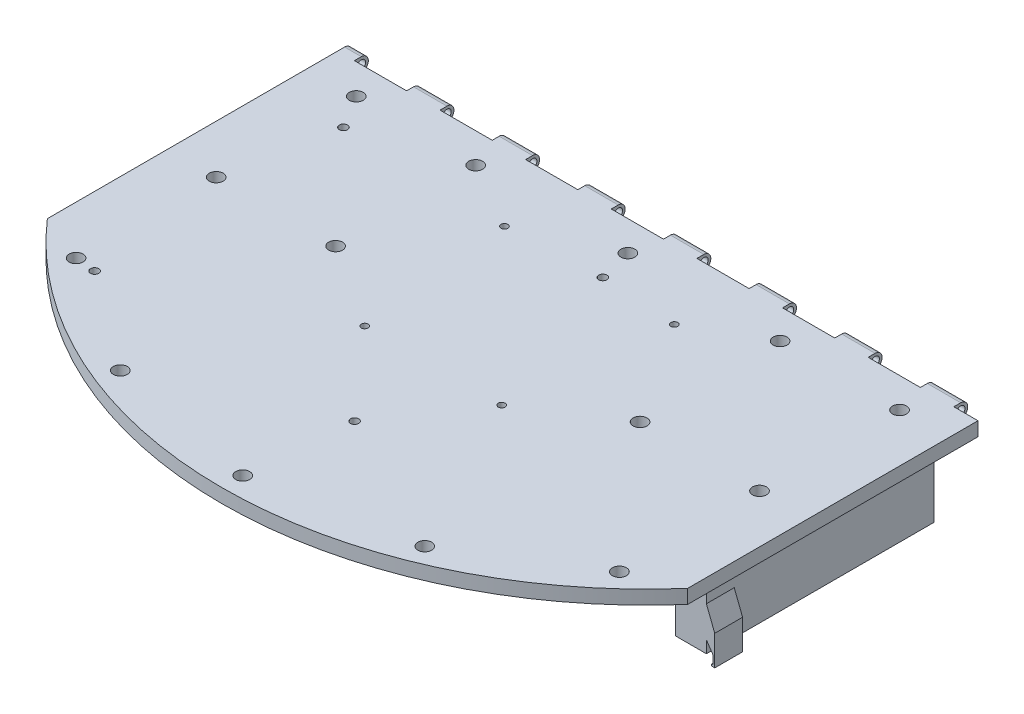
SolidWorks part; units mm, degrees
ref_plane "Front Plane" through (0, 0, 0) normal (0, 0, 1) x (1, 0, 0)
ref_plane "Top Plane" through (0, 0, 0) normal (0, 1, 0) x (1, 0, 0)
ref_plane "Right Plane" through (0, 0, 0) normal (1, 0, 0) x (0, 0, -1)
sketch "Sketch1" plane through (0, 0, 0) normal (0, 1, 0) x (1, 0, 0)
  line L0 (154.8848, 4.1371) -> (-154.8848, 4.1371)
  circle A0 centre (0, 0) radius 154.94
  arc A1 (154.8848, 4.1371) -> (-154.8848, 4.1371) centre (0, 0) cw
  dimension "D1" = 309.88
extrude "Boss-Extrude1" add sketch "Sketch1" along normal blind 5.08 contours L0 A0
sketch "Sketch2" plane through (0, 0, 0) normal (0, -1, 0) x (-1, 0, 0)
  line L0 (0, -154.94) -> (0, 4.1371) construction
  line L1 (-154.8848, 4.1371) -> (154.8848, 4.1371) construction
  line L8 (-112.1983, -7.3509) -> (-100.8687, -7.3509)
  line L9 (112.1983, -90.3509) -> (100.8687, -90.3509)
  line L10 (112.1983, -90.3509) -> (112.1983, -7.3509)
  line L11 (112.1983, -7.3509) -> (100.8687, -7.3509)
  line L12 (100.8687, -90.3509) -> (100.8687, -7.3509)
  line L13 (-112.1983, -90.3509) -> (-112.1983, -7.3509)
  line L14 (-112.1983, -90.3509) -> (-100.8687, -90.3509)
  line L15 (-100.8687, -90.3509) -> (-100.8687, -7.3509)
  arc A0 (-154.8848, 4.1371) -> (154.8848, 4.1371) centre (0, 0) ccw construction
extrude "Boss-Extrude2" add sketch "Sketch2" along normal blind 23.622
sketch "Sketch3" plane through (0, 0, 0) normal (1, 0, 0) x (0, 0, -1)
  line L1 (4.1371, 5.08) -> (6.6771, 5.08)
  line L2 (4.1371, 5.08) -> (4.1371, 0)
  line L3 (4.1371, 0) -> (6.6771, 0)
  line L4 (6.6771, 5.08) -> (6.6771, 0)
  circle A0 centre (6.6771, 2.54) radius 2.54
extrude "Boss-Extrude3" add sketch "Sketch3" against normal up to vertex (154.8848 mm away) and the other way up to vertex (154.8848 mm away) contours L4 A0 | A0 L1 L2 | L4 A0 | A0 L2 L3
sketch "Sketch4" plane through (0, 5.08, 0) normal (0, 1, 0) x (1, 0, 0)
  line L0 (-154.8848, 4.1371) -> (-154.8848, 6.6771) construction
  line L1 (-141.9541, 9.2171) -> (-122.9041, 9.2171)
  line L2 (-141.9541, 9.2171) -> (-141.9541, 4.1371)
  line L3 (-141.9541, 4.1371) -> (-122.9041, 4.1371)
  line L4 (-122.9041, 9.2171) -> (-122.9041, 4.1371)
  line L5 (-110.7121, 9.2171) -> (-110.7121, 4.1371)
  line L6 (-110.7121, 9.2171) -> (-91.6621, 9.2171)
  line L7 (-91.6621, 9.2171) -> (-91.6621, 4.1371)
  line L8 (-110.7121, 4.1371) -> (-91.6621, 4.1371)
  line L9 (-79.4701, 9.2171) -> (-79.4701, 4.1371)
  line L10 (-79.4701, 9.2171) -> (-60.4201, 9.2171)
  line L11 (-60.4201, 9.2171) -> (-60.4201, 4.1371)
  line L12 (-79.4701, 4.1371) -> (-60.4201, 4.1371)
  line L13 (-48.2281, 9.2171) -> (-48.2281, 4.1371)
  line L14 (-48.2281, 9.2171) -> (-29.1781, 9.2171)
  line L15 (-29.1781, 9.2171) -> (-29.1781, 4.1371)
  line L16 (-48.2281, 4.1371) -> (-29.1781, 4.1371)
  line L17 (-16.9861, 9.2171) -> (-16.9861, 4.1371)
  line L18 (-16.9861, 9.2171) -> (2.0639, 9.2171)
  line L19 (2.0639, 9.2171) -> (2.0639, 4.1371)
  line L20 (-16.9861, 4.1371) -> (2.0639, 4.1371)
  line L21 (14.2559, 9.2171) -> (14.2559, 4.1371)
  line L22 (14.2559, 9.2171) -> (33.3059, 9.2171)
  line L23 (33.3059, 9.2171) -> (33.3059, 4.1371)
  line L24 (14.2559, 4.1371) -> (33.3059, 4.1371)
  line L25 (45.4979, 9.2171) -> (45.4979, 4.1371)
  line L26 (45.4979, 9.2171) -> (64.5479, 9.2171)
  line L27 (64.5479, 9.2171) -> (64.5479, 4.1371)
  line L28 (45.4979, 4.1371) -> (64.5479, 4.1371)
  line L29 (76.7399, 9.2171) -> (76.7399, 4.1371)
  line L30 (76.7399, 9.2171) -> (95.7899, 9.2171)
  line L31 (95.7899, 9.2171) -> (95.7899, 4.1371)
  line L32 (76.7399, 4.1371) -> (95.7899, 4.1371)
  line L33 (107.9819, 9.2171) -> (107.9819, 4.1371)
  line L34 (107.9819, 9.2171) -> (127.0319, 9.2171)
  line L35 (127.0319, 9.2171) -> (127.0319, 4.1371)
  line L36 (107.9819, 4.1371) -> (127.0319, 4.1371)
  line L37 (139.2239, 9.2171) -> (139.2239, 4.1371)
  line L38 (139.2239, 9.2171) -> (158.2739, 9.2171)
  line L39 (158.2739, 9.2171) -> (158.2739, 4.1371)
  line L40 (139.2239, 4.1371) -> (158.2739, 4.1371)
  dimension "D1" = 19.05
  dimension "D3" = 5.08
  dimension "D4" = 12.9307
  dimension "D2" = 10
extrude "Cut-Extrude2" cut sketch "Sketch4" against normal up to surface (5.08 mm away) up to face at (-106.5335, 0, 48.8509)
sketch "Sketch5" plane through (0, 5.08, 0) normal (0, 1, 0) x (1, 0, 0)
  line L0 (31, -20.8309) -> (-31, -20.8309) construction
  line L3 (25, -77.8309) -> (-25, -77.8309) construction
  circle A0 centre (-31, -20.8309) radius 1.25
  circle A1 centre (-25, -77.8309) radius 1.25
  circle A2 centre (31, -20.8309) radius 1.25
  circle A3 centre (25, -77.8309) radius 1.25
  point P8 (0, -20.8309)
  point P9 (0, -77.8309)
  dimension "D3" = 2.5
  dimension "D1" = 57
  dimension "D2" = 62
  dimension "D4" = 50
extrude "Cut-Extrude3" cut sketch "Sketch5" against normal up to surface (5.08 mm away) up to face at (-3.5375, 0, -1.4962)
sketch "Sketch6" plane through (0, 5.08, 0) normal (0, 1, 0) x (1, 0, 0)
  line L0 (-116.8081, 9.2171) -> (-116.8081, -101.7953) construction
  line L18 (-110.7121, 9.2171) -> (-122.9041, 9.2171) construction
  line L19 (0, -55) -> (0, 55) construction
  line L20 (116.8081, 9.2171) -> (116.8081, -101.7953) construction
  line L21 (116.8081, 14.4309) -> (204.1863, 14.4309)
  line L22 (-116.8081, -101.7953) -> (-204.1863, -101.7953)
  line L23 (-116.8081, -101.7953) -> (-116.8081, 14.4309)
  line L24 (-116.8081, 14.4309) -> (-204.1863, 14.4309)
  line L25 (-204.1863, -101.7953) -> (-204.1863, 14.4309)
  line L26 (204.1863, -101.7953) -> (204.1863, 14.4309)
  line L27 (116.8081, -101.7953) -> (204.1863, -101.7953)
  line L28 (116.8081, -101.7953) -> (116.8081, 14.4309)
  arc A1 (-154.8848, 4.1371) -> (154.8848, 4.1371) centre (0, 0) ccw construction
ref_plane "Plane1" through (0, 0, 0) normal (1, 0, 0) x (0, 0, -1)
extrude "Cut-Extrude5" cut sketch "Sketch6" against normal up to surface (5.08 mm away) up to face at (-31, 0, 22.0809)
sketch "Sketch7" plane through (0, 5.08, 0) normal (0, 1, 0) x (1, 0, 0)
  line L1 (55.5438, -6.7887) -> (-55.5438, -6.7887) construction
  line L2 (55.5438, -6.7887) -> (55.5438, -136.448) construction
  line L3 (55.5438, -136.448) -> (-55.5438, -136.448) construction
  line L4 (-55.5438, -6.7887) -> (-55.5438, -136.448) construction
  line L5 (-99.1141, -6.7887) -> (99.1141, -6.7887) construction
  line L6 (-99.1141, -6.7887) -> (-99.1141, -108.9934) construction
  line L7 (-99.1141, -108.9934) -> (99.1141, -108.9934) construction
  line L8 (99.1141, -6.7887) -> (99.1141, -108.9934) construction
  circle A0 centre (0, -147.32) radius 2.54
  circle A1 centre (0, -6.7887) radius 2.54
  circle A2 centre (55.5438, -136.448) radius 2.54
  circle A3 centre (-55.5438, -136.448) radius 2.54
  circle A4 centre (-99.1141, -108.9934) radius 2.54
  circle A5 centre (-99.1141, -6.7887) radius 2.54
  circle A6 centre (99.1141, -6.7887) radius 2.54
  circle A7 centre (-55.5438, -6.7887) radius 2.54
  circle A8 centre (55.5438, -6.7887) radius 2.54
  circle A9 centre (99.1141, -108.9934) radius 2.54
  circle A10 centre (-99.1141, -57.8911) radius 2.54
  circle A11 centre (99.1141, -57.8911) radius 2.54
  circle A12 centre (55.5438, -57.8911) radius 2.54
  circle A13 centre (-55.5438, -57.8911) radius 2.54
  point P12 (0, -6.7887)
  point P16 (0, -6.7887)
  dimension "D5" = 5.08
  dimension "D1" = 147.32
  dimension "D2" = 147.32
  dimension "D3" = 147.32
  dimension "D4" = 99.1141
extrude "Cut-Extrude6" cut sketch "Sketch7" against normal up to surface (5.08 mm away) up to face at (-31, 0, 22.0809)
sketch "Sketch8" plane through (107.9819, 0, 0) normal (1, 0, 0) x (0, 0, -1)
  circle A0 centre (6.6771, 2.54) radius 1.55
extrude "Cut-Extrude7" cut sketch "Sketch8" against normal up to surface (224.79 mm away) up to face at (-116.8081, 2.54, 46.9241)
sketch "Sketch9" plane through (0, 0, 90.3509) normal (0, 0, 1) x (1, 0, 0)
  line L0 (112.1983, -23.622) -> (112.1983, 0) construction
  line L1 (112.1983, -15.6335) -> (115.2463, -15.6335)
  line L2 (112.1983, -15.6335) -> (112.1983, -22.7455)
  line L3 (112.1983, -22.7455) -> (115.2463, -22.7455)
  line L4 (115.2463, -15.6335) -> (115.2463, -22.7455)
  line L5 (114.6113, -25.7784) -> (114.1033, -25.8863)
  line L6 (115.2463, -22.7455) -> (114.6113, -22.7455)
  line L7 (115.2463, -22.7455) -> (115.2463, -26.1745)
  line L8 (115.2463, -26.1745) -> (114.6113, -26.1745)
  line L9 (114.6113, -22.7455) -> (114.6113, -26.1745)
  line L10 (114.1033, -25.8863) -> (114.1033, -26.4626)
  line L11 (114.1033, -26.1745) -> (114.6113, -26.1745)
  line L12 (112.1983, -19.1895) -> (114.6113, -22.7455)
  line L13 (114.6113, -26.5706) -> (114.1033, -26.4626)
  line L14 (114.6113, -25.7784) -> (115.2463, -25.7784)
  line L15 (114.6113, -25.7784) -> (114.6113, -26.5706)
  line L16 (114.6113, -26.1745) -> (115.2463, -26.1745)
  line L17 (115.2463, -25.7784) -> (115.2463, -26.5706)
  line L18 (114.6113, -26.5706) -> (115.2463, -26.5706)
  line L19 (0, -15.7861) -> (0, 15.7861) construction
  line L20 (-115.2463, -25.7784) -> (-115.2463, -26.5706)
  line L21 (-114.6113, -26.5706) -> (-115.2463, -26.5706)
  line L22 (-114.6113, -26.5706) -> (-114.1033, -26.4626)
  line L23 (-114.1033, -25.8863) -> (-114.1033, -26.4626)
  line L24 (-114.6113, -25.7784) -> (-114.1033, -25.8863)
  line L25 (-115.2463, -26.1745) -> (-114.6113, -26.1745)
  line L26 (-114.6113, -25.7784) -> (-115.2463, -25.7784)
  line L27 (-115.2463, -22.7455) -> (-115.2463, -26.1745)
  line L28 (-114.6113, -22.7455) -> (-114.6113, -26.1745)
  line L29 (-112.1983, -19.1895) -> (-114.6113, -22.7455)
  line L30 (-112.1983, -22.7455) -> (-115.2463, -22.7455)
  line L31 (-115.2463, -15.6335) -> (-115.2463, -22.7455)
  line L32 (-112.1983, -15.6335) -> (-115.2463, -15.6335)
  line L33 (-112.1983, -15.6335) -> (-112.1983, -22.7455)
  line L39 (-112.1983, -15.6335) -> (-115.2463, -15.6335)
  line L42 (112.1983, -15.6335) -> (115.2463, -15.6335)
  line L49 (112.1983, -15.6335) -> (112.1983, -11.811)
  dimension "D1" = 3.429
  dimension "D2" = 7.112
  dimension "D3" = 3.048
  dimension "D4" = 2.413
  dimension "D5" = 0.508
  dimension "D6" = 0.3961
  dimension "D7" = 0.2882
extrude "Boss-Extrude4" add sketch "Sketch9" against normal blind 10.16 contours L2 L12 L3 L4 L1 | L9 L14 L7 L3 | L10 L11 L9 L5 | L14 L9 L8 L7 | L15 L18 L17 L8 | L15 L11 L10 L13 | L33 L32 L31 L30 L29 | L28 L30 L27 L26 | L28 L26 L20 L25 | L24 L28 L25 L20 L21 L22 L23
sketch "Sketch11" plane through (0, 0, 90.3509) normal (0, 0, 1) x (1, 0, 0)
  line L0 (112.1983, -7.8167) -> (115.2463, -15.6335)
  line L1 (112.1983, -15.6335) -> (112.1983, 0) construction
  line L2 (115.2463, -15.6335) -> (115.2463, -26.5706) construction
  line L3 (115.2463, -15.6335) -> (112.1983, -15.6335)
  line L4 (112.1983, -15.6335) -> (115.2463, -15.6335) construction
  line L5 (112.1983, -15.6335) -> (112.1983, -7.8167)
  line L6 (0, -17.4078) -> (0, 17.4078) construction
  line L7 (-115.2463, -15.6335) -> (-112.1983, -15.6335)
  line L8 (-112.1983, -7.8167) -> (-115.2463, -15.6335)
  line L9 (-112.1983, -15.6335) -> (-112.1983, -7.8167)
extrude "Boss-Extrude5" add sketch "Sketch11" against normal up to surface (10.16 mm away) up to face at (114.1033, -22.7189, 80.1909)
sketch "Sketch12" plane through (0, 5.08, 0) normal (0, 1, 0) x (1, 0, 0)
  circle A0 centre (-91.6461, -18.9209) radius 1.5
  circle A1 centre (-91.6461, -109.7109) radius 1.5
  circle A2 centre (3.2079, -109.7109) radius 1.5
  circle A3 centre (3.0945, -19.0343) radius 1.5
extrude "Cut-Extrude8" cut sketch "Sketch12" against normal up to surface (5.08 mm away) up to face at (0, 0, 149.86)
